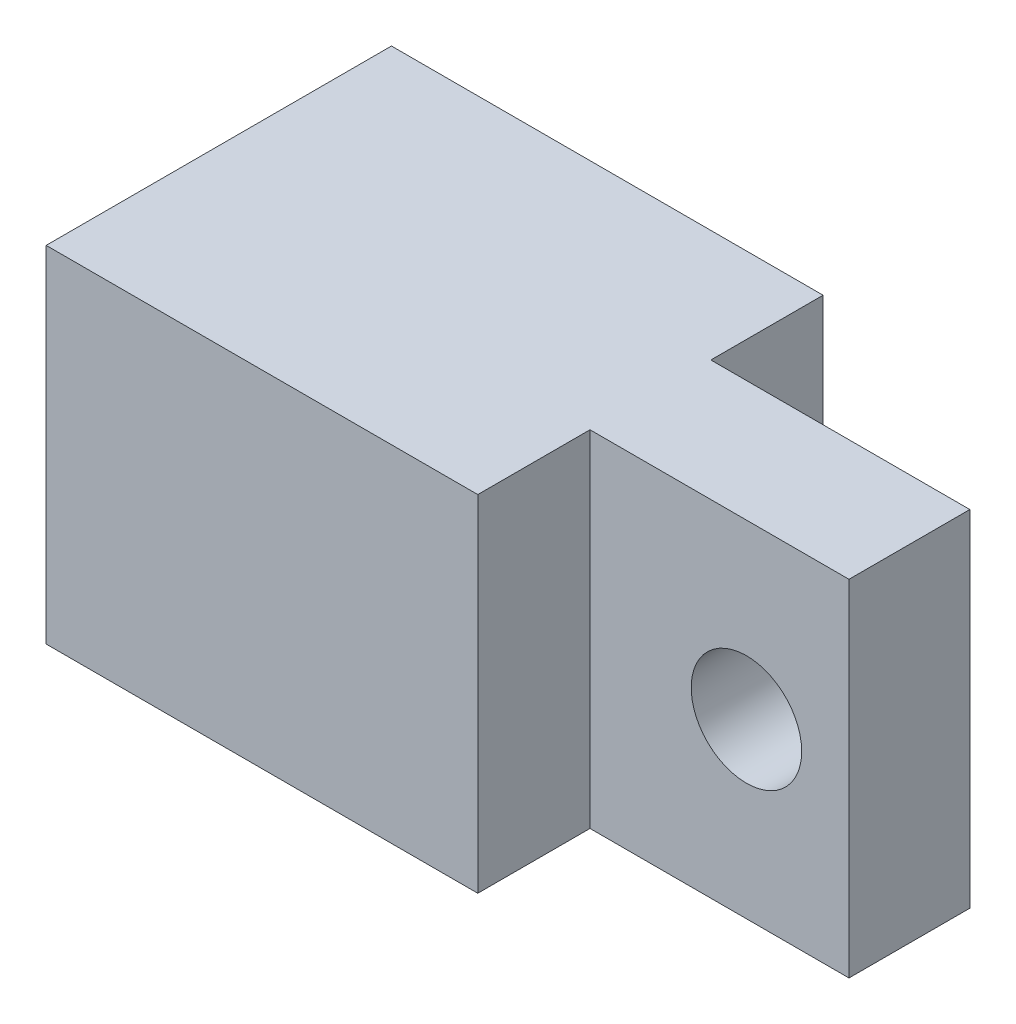
SolidWorks part; units mm, degrees
ref_plane "Front Plane" through (0, 0, 0) normal (0, 0, 1) x (1, 0, 0)
ref_plane "Top Plane" through (0, 0, 0) normal (0, 1, 0) x (1, 0, 0)
ref_plane "Right Plane" through (0, 0, 0) normal (1, 0, 0) x (0, 0, -1)
sketch "Sketch1" plane through (0, 0, 0) normal (0, 1, 0) x (1, 0, 0)
  line L0 (6.25, 5) -> (6.25, 1.75)
  line L1 (6.25, -5) -> (-6.25, -5)
  line L3 (6.25, 5) -> (-6.25, 5)
  line L4 (-6.25, -5) -> (-6.25, 5)
  line L5 (6.25, -1.75) -> (13.75, -1.75)
  line L11 (6.25, 1.75) -> (13.75, 1.75)
  line L12 (13.75, -1.75) -> (13.75, 1.75)
  line L17 (6.25, 0) -> (13.75, 1.75) construction
  line L18 (6.25, 0) -> (13.75, -1.75) construction
  line L23 (6.25, -1.75) -> (6.25, -5)
  point P0 (0, 0)
  point P5 (6.25, 0)
  dimension "D1" = 12.5
  dimension "D2" = 3.5
  dimension "D3" = 7.5
extrude "Boss-Extrude1" add sketch "Sketch1" along normal blind 10
sketch "Sketch4" plane through (0, 0, 1.75) normal (0, 0, 1) x (1, 0, 0)
  circle A0 centre (10.7803, 5) radius 1.6
  dimension "D1" = 3.2
extrude "Cut-Extrude2" cut sketch "Sketch4" against normal through all
